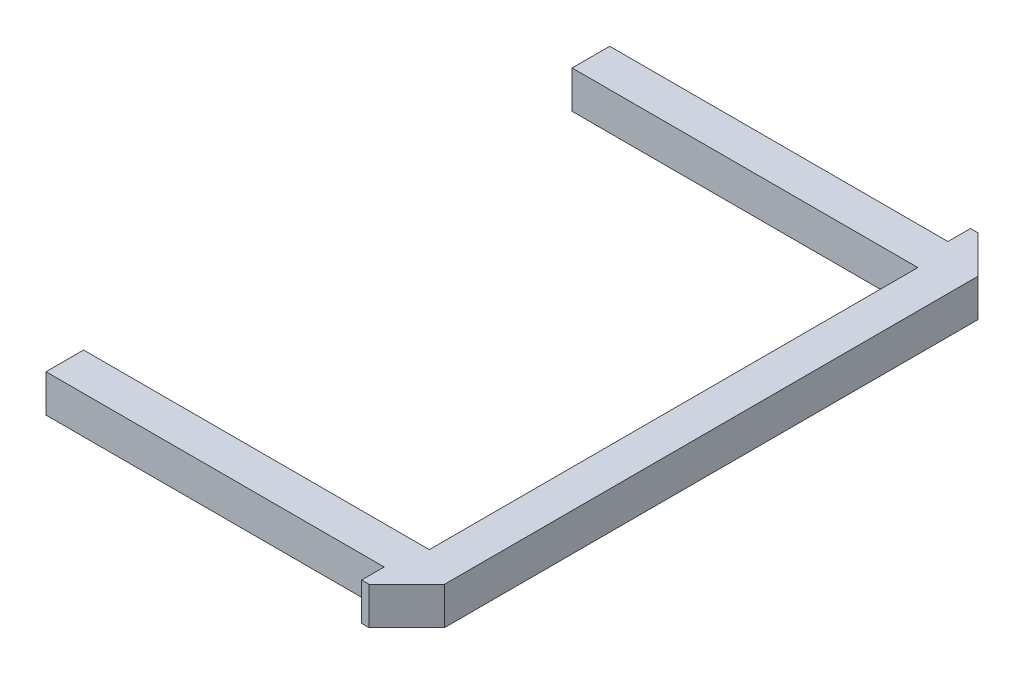
SolidWorks part; units mm, degrees
ref_plane "Front Plane" through (0, 0, 0) normal (0, 0, 1) x (1, 0, 0)
ref_plane "Top Plane" through (0, 0, 0) normal (0, 1, 0) x (1, 0, 0)
ref_plane "Right Plane" through (0, 0, 0) normal (1, 0, 0) x (0, 0, -1)
sketch "Sketch1" plane through (0, 0, 0) normal (0, 1, 0) x (1, 0, 0)
  line L0 (38.2771, -125.6555) -> (83.2771, -125.6555)
  line L1 (83.2771, -125.6555) -> (83.2771, -122.6555)
  line L2 (83.2771, -122.6555) -> (84.2771, -122.6555)
  line L3 (84.2771, -122.6555) -> (89.2771, -127.6555)
  line L4 (89.2771, -127.6555) -> (89.2771, -198.6555)
  line L5 (89.2771, -198.6555) -> (84.2771, -203.6555)
  line L6 (84.2771, -203.6555) -> (83.2771, -203.6555)
  line L7 (83.2771, -203.6555) -> (83.2771, -200.6555)
  line L8 (83.2771, -200.6555) -> (38.2771, -200.6555)
  line L9 (38.2771, -130.6555) -> (84.2771, -130.6555)
  line L10 (84.2771, -130.6555) -> (84.2771, -130.6555)
  line L11 (84.2771, -130.6555) -> (84.2771, -130.6555)
  line L12 (84.2771, -130.6555) -> (84.2771, -130.6555)
  line L13 (84.2771, -130.6555) -> (84.2771, -195.6555)
  line L14 (84.2771, -195.6555) -> (84.2771, -195.6555)
  line L15 (84.2771, -195.6555) -> (84.2771, -195.6555)
  line L16 (84.2771, -195.6555) -> (84.2771, -195.6555)
  line L17 (84.2771, -195.6555) -> (38.2771, -195.6555)
  line L18 (38.2771, -125.6555) -> (38.2771, -130.6555)
  line L19 (38.2771, -195.6555) -> (38.2771, -200.6555)
  dimension "D2" = 46
  dimension "D3" = 46
  dimension "D1" = 5
extrude "Boss-Extrude1" add sketch "Sketch1" along normal blind 5 contours L9 L10 L11 L12 L13 L14 L15 L16 L17 L19 L8 L7 L6 L5 L4 L3 L2 L1 L0 L18
